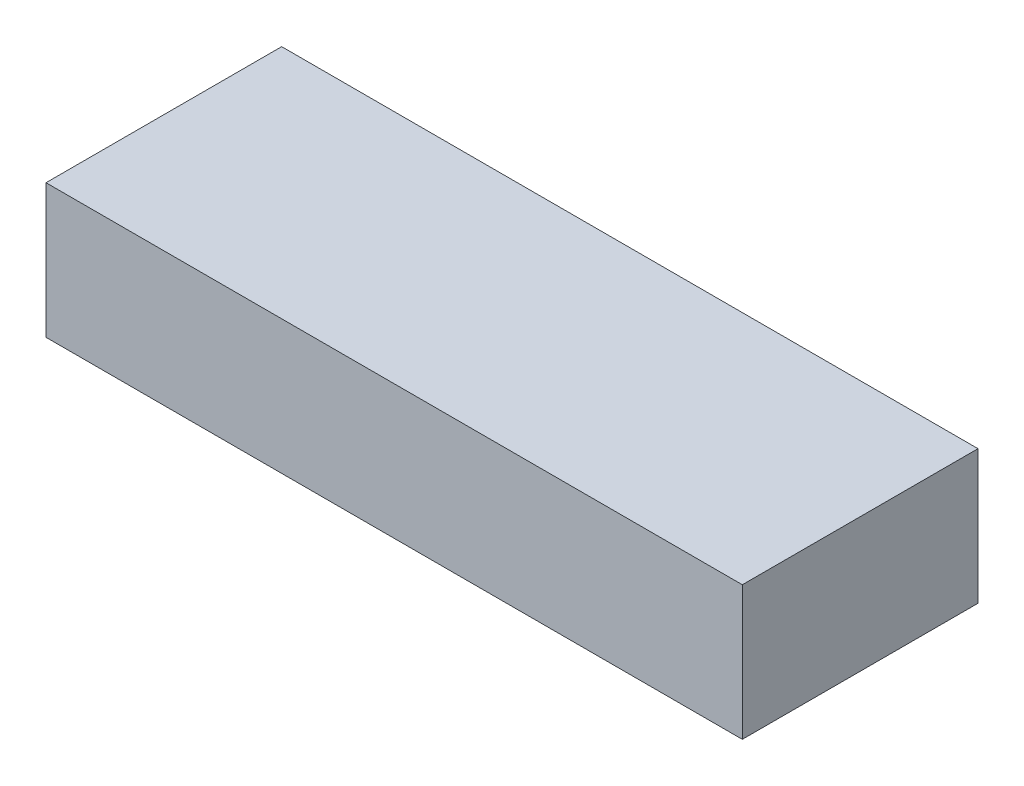
SolidWorks part; units mm, degrees
ref_plane "Front Plane" through (0, 0, 0) normal (0, 0, 1) x (1, 0, 0)
ref_plane "Top Plane" through (0, 0, 0) normal (0, 1, 0) x (1, 0, 0)
ref_plane "Right Plane" through (0, 0, 0) normal (1, 0, 0) x (0, 0, -1)
sketch "Sketch1" plane through (0, 0, 0) normal (0, 1, 0) x (1, 0, 0)
  line L1 (-38.9895, -22.1158) -> (91.0105, -22.1158)
  line L2 (-38.9895, -22.1158) -> (-38.9895, 21.8842)
  line L3 (-38.9895, 21.8842) -> (91.0105, 21.8842)
  line L4 (91.0105, -22.1158) -> (91.0105, 21.8842)
  dimension "D1" = 44
  dimension "D2" = 130
extrude "Boss-Extrude1" add sketch "Sketch1" along normal blind 25
